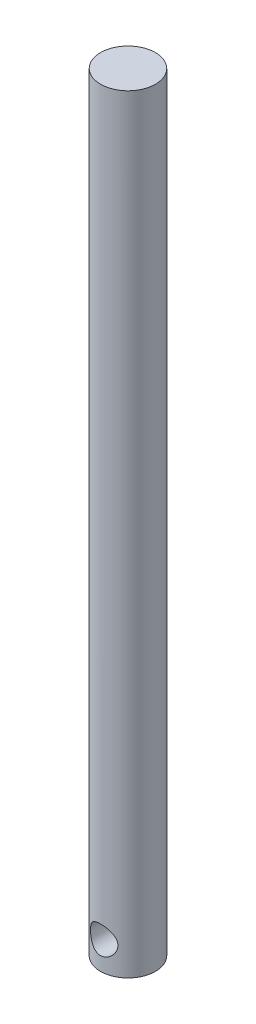
SolidWorks part; units mm, degrees
ref_plane "Front" through (0, 0, 0) normal (0, 0, 1) x (1, 0, 0)
ref_plane "Top" through (0, 0, 0) normal (0, 1, 0) x (1, 0, 0)
ref_plane "Right" through (0, 0, 0) normal (1, 0, 0) x (0, 0, -1)
sketch "Sketch1" plane through (0, 0, 0) normal (0, 1, 0) x (1, 0, 0)
  circle A0 centre (0, 0) radius 6.35
  dimension "D1" = 12.7
extrude "Boss-Extrude1" add sketch "Sketch1" along normal blind 177.8
sketch "Sketch2" plane through (0, 0, 0) normal (0, 0, 1) x (1, 0, 0)
  circle A0 centre (0, 6.35) radius 3.175
  dimension "D1" = 6.35
  dimension "D2" = 6.35
extrude "Cut-Extrude1" cut sketch "Sketch2" against normal through all both and the other way through all
